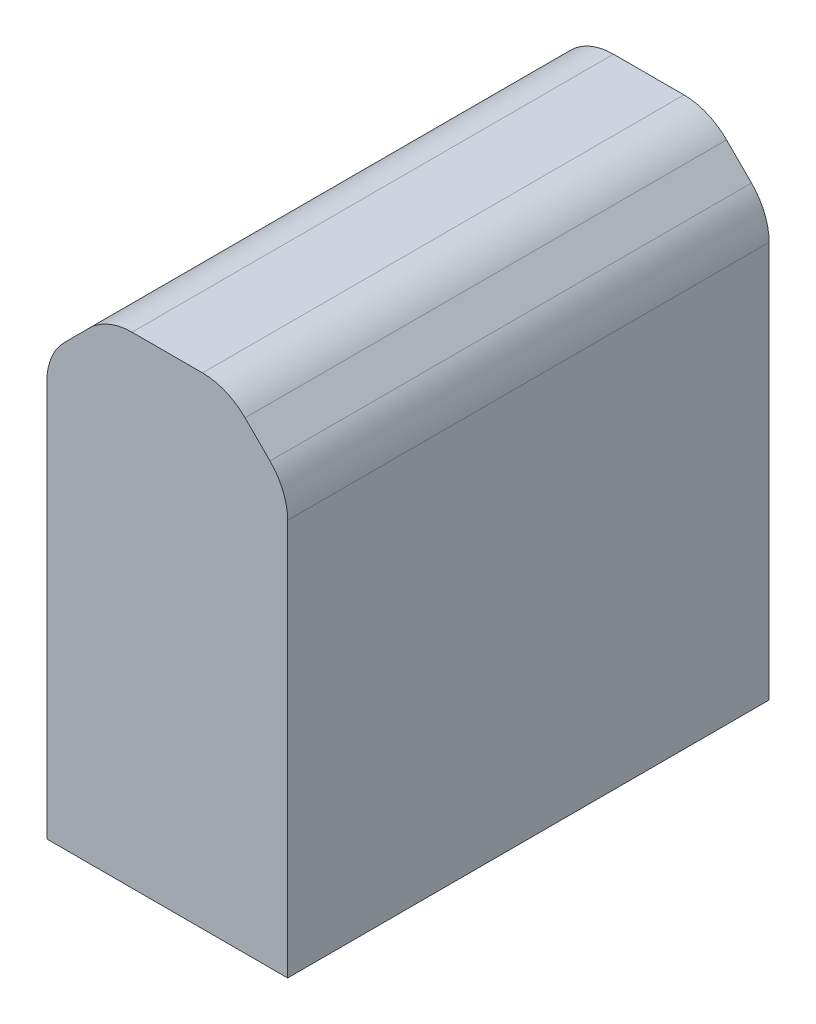
SolidWorks part; units mm, degrees
ref_plane "Front Plane" through (0, 0, 0) normal (0, 0, 1) x (1, 0, 0)
ref_plane "Top Plane" through (0, 0, 0) normal (0, 1, 0) x (1, 0, 0)
ref_plane "Right Plane" through (0, 0, 0) normal (1, 0, 0) x (0, 0, -1)
sketch "Sketch1" plane through (0, 0, 0) normal (0, 1, 0) x (1, 0, 0)
  line L1 (-1, 2) -> (1, 2)
  line L2 (-1, 2) -> (-1, -2)
  line L3 (-1, -2) -> (1, -2)
  line L4 (1, 2) -> (1, -2)
  line L5 (-1, 2) -> (1, -2) construction
  line L6 (-1, -2) -> (1, 2) construction
  point P0 (0, 0)
  dimension "D1" = 2
  dimension "D2" = 4
extrude "Boss-Extrude1" add sketch "Sketch1" along normal blind 4
chamfer "Chamfer1" distance 0.5 angle 45 2 edges at (-1, 4, 0) (1, 4, 0)
fillet "Fillet1" radius 0.5 4 edges at (-1, 3.5, 0) (-0.5, 4, 0) (1, 3.5, 0) (0.5, 4, 0)
